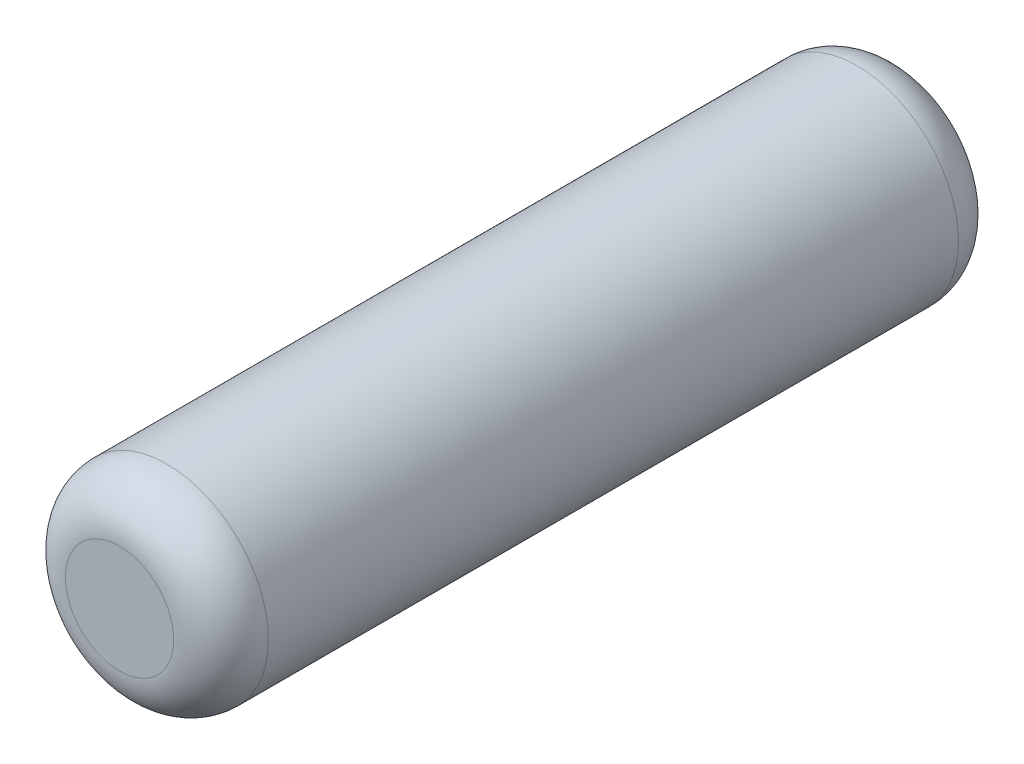
SolidWorks part; units mm, degrees
ref_plane "Front" through (0, 0, 0) normal (0, 0, 1) x (1, 0, 0)
ref_plane "Top" through (0, 0, 0) normal (0, 1, 0) x (1, 0, 0)
ref_plane "Right" through (0, 0, 0) normal (1, 0, 0) x (0, 0, -1)
sketch "Sketch1" plane through (0, 0, 0) normal (0, 0, 1) x (1, 0, 0)
  circle A0 centre (0, 0) radius 0.75
  dimension "D1" = 1.5
extrude "Boss-Extrude1" add sketch "Sketch1" along normal mid plane 5.8
fillet "Fillet1" radius 0.35 2 edges at (0.75, 0, -2.9) (0.75, 0, 2.9)
